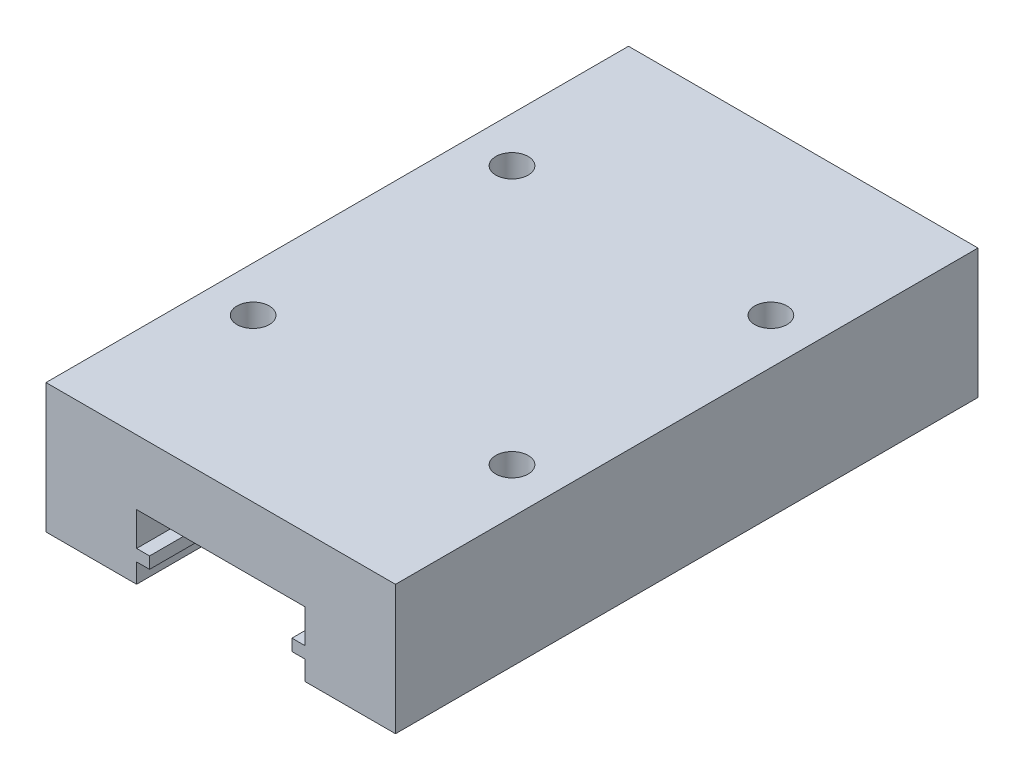
SolidWorks part; units mm, degrees
ref_plane "Plan de face" through (0, 0, 0) normal (0, 0, 1) x (1, 0, 0)
ref_plane "Plan de dessus" through (0, 0, 0) normal (0, 1, 0) x (1, 0, 0)
ref_plane "Plan de droite" through (0, 0, 0) normal (1, 0, 0) x (0, 0, -1)
sketch "Esquisse1" plane through (0, 0, 0) normal (0, 0, 1) x (1, 0, 0)
  line L0 (6.5, -5) -> (13.5, -5)
  line L1 (-13.5, -5) -> (-6.5, -5)
  line L2 (-13.5, -5) -> (-13.5, 5)
  line L3 (-13.5, 5) -> (13.5, 5)
  line L4 (13.5, -5) -> (13.5, 5)
  line L5 (-13.5, -5) -> (13.5, 5) construction
  line L6 (-13.5, 5) -> (13.5, -5) construction
  line L8 (-6.5, -5) -> (-6.5, -3.5)
  line L9 (-6.5, 0) -> (6.5, 0)
  line L10 (6.5, -5) -> (6.5, -3.5)
  line L11 (-6.5, -2.6) -> (-6.5, 0)
  line L12 (-6.5, -2.6) -> (-5.5, -2.6)
  line L14 (-6.5, -3.5) -> (-5.5, -3.5)
  line L15 (-5.5, -2.6) -> (-5.5, -3.5)
  line L16 (0, -55) -> (0, 55) construction
  line L17 (6.5, -3.5) -> (5.5, -3.5)
  line L18 (5.5, -2.6) -> (5.5, -3.5)
  line L19 (6.5, -2.6) -> (5.5, -2.6)
  line L20 (6.5, -2.6) -> (6.5, 0)
  point P0 (0, 0)
  dimension "D1" = 27
  dimension "D2" = 10
  dimension "D3" = 7
  dimension "D4" = 1.5
  dimension "D5" = 0.9
  dimension "D6" = 1
  dimension "D7" = 5
extrude "Boss.-Extru.1" add sketch "Esquisse1" along normal mid plane 45
hole_wizard "Trou pour taraudage pour trou taraudé M3x0.51" positions "Esquisse2" profile "Esquisse3" hole size "M3x0.5" standard "Ansi Metric"
sketch "Esquisse2" plane through (0, 5, 0) normal (0, 1, 0) x (1, 0, 0)
  line L0 (13.5, 22.5) -> (-13.5, 22.5) construction
  line L1 (-13.5, -22.5) -> (-13.5, 22.5) construction
  line L3 (-5.5, 0) -> (5.5, 0) construction
  line L4 (0, -5.5) -> (0, 5.5) construction
  point P0 (-10, 10)
  point P11 (-10, -10)
  point P14 (10, -10)
  point P15 (10, 10)
  point P16 (0, 0)
  dimension "D1" = 12.5
  dimension "D2" = 3.5
sketch "Esquisse3" plane through (-10, 5, -10) normal (1, 0, 0) x (0, 0, 1)
  line L0 (0, 0) -> (0, 5.7511)
  line L1 (0, 5.7511) -> (1.25, 5)
  line L2 (1.25, 5) -> (1.25, 0)
  line L5 (1.25, 0) -> (0, 0)
  line L10 (0, 5.7511) -> (-1.25, 5) construction
  line L11 (0, -6.35) -> (0, 107.95) construction
  dimension "Diamètre du perçage" = 2.5
  dimension "Profondeur du perçage" = 5
  dimension "Angle de pointe" = 118
